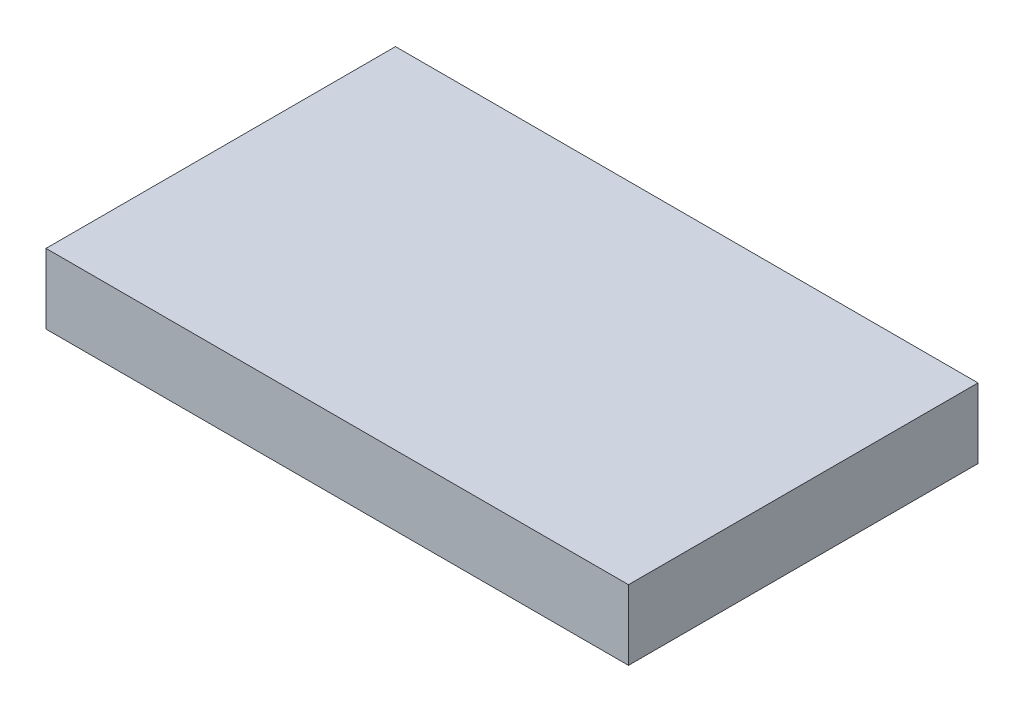
SolidWorks part; units mm, degrees
material "Maple"
ref_plane "Front Plane" through (0, 0, 0) normal (0, 0, 1) x (1, 0, 0)
ref_plane "Top Plane" through (0, 0, 0) normal (0, 1, 0) x (1, 0, 0)
ref_plane "Right Plane" through (0, 0, 0) normal (1, 0, 0) x (0, 0, -1)
sketch "Sketch1" plane through (0, 0, 0) normal (0, 1, 0) x (1, 0, 0)
  line L1 (-25, 15) -> (25, 15)
  line L2 (-25, 15) -> (-25, -15)
  line L3 (-25, -15) -> (25, -15)
  line L4 (25, 15) -> (25, -15)
  line L5 (-25, 15) -> (25, -15) construction
  line L6 (-25, -15) -> (25, 15) construction
  point P0 (0, 0)
  dimension "D1" = 50
  dimension "D2" = 30
extrude "Boss-Extrude1" add sketch "Sketch1" along normal blind 6
ref_plane "Plane1" through (0, 3, 0) normal (0, 1, 0) x (1, 0, 0)
